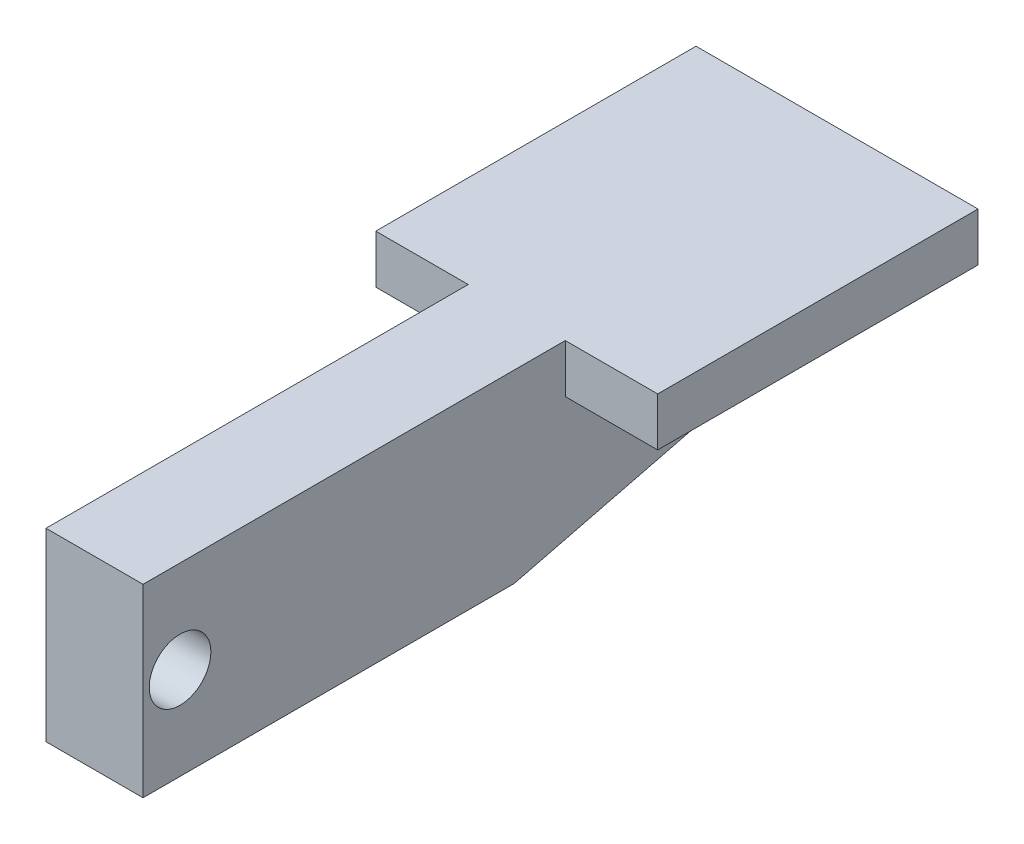
SolidWorks part; units mm, degrees
ref_plane "Front Plane" through (0, 0, 0) normal (0, 0, 1) x (1, 0, 0)
ref_plane "Top Plane" through (0, 0, 0) normal (0, 1, 0) x (1, 0, 0)
ref_plane "Right Plane" through (0, 0, 0) normal (1, 0, 0) x (0, 0, -1)
sketch "Sketch1" plane through (0, 0, 0) normal (1, 0, 0) x (0, 0, -1)
  line L0 (0, -19.05) -> (76.5, 0)
  line L1 (-76.5, 19.05) -> (76.5, 19.05)
  line L2 (-76.5, 19.05) -> (-76.5, -19.05)
  line L3 (-76.5, -19.05) -> (0, -19.05)
  line L4 (76.5, 19.05) -> (76.5, 0)
  line L5 (-76.5, 19.05) -> (38.25, -9.525) construction
  line L6 (-76.5, -19.05) -> (76.5, 19.05) construction
  point P0 (0, 0)
  dimension "D1" = 76.5
  dimension "D2" = 76.5
  dimension "D3" = 19.05
  dimension "D4" = 38.1
  dimension "D5" = 153
extrude "Boss-Extrude1" add sketch "Sketch1" along normal blind 20
sketch "Sketch3" plane through (20, 0, 0) normal (1, 0, 0) x (0, 0, -1)
  line L1 (76.5, 19.05) -> (10.5, 19.05)
  line L2 (76.5, 19.05) -> (76.5, 9.05)
  line L3 (76.5, 9.05) -> (10.5, 9.05)
  line L4 (10.5, 19.05) -> (10.5, 9.05)
  dimension "D1" = 66
  dimension "D2" = 10
extrude "Boss-Extrude2" add sketch "Sketch3" along normal blind 19.05
sketch "Sketch4" plane through (0, 0, 0) normal (-1, 0, 0) x (0, 0, 1)
  line L1 (-76.5, 19.05) -> (-10.5, 19.05)
  line L2 (-76.5, 19.05) -> (-76.5, 9.05)
  line L3 (-76.5, 9.05) -> (-10.5, 9.05)
  line L4 (-10.5, 19.05) -> (-10.5, 9.05)
  dimension "D1" = 66
  dimension "D2" = 10
extrude "Boss-Extrude3" add sketch "Sketch4" along normal blind 19.05
sketch "Sketch5" plane through (20, 0, 0) normal (1, 0, 0) x (0, 0, -1)
  line L0 (-76.5, 19.05) -> (-76.5, -19.05) construction
  circle A0 centre (-68.88, 0) radius 6.35
  point P4 (-76.5, 0)
  dimension "D2" = 12.7
  dimension "D1" = 7.62
  dimension "D3" = 19.05
extrude "Cut-Extrude2" cut sketch "Sketch5" against normal through all
